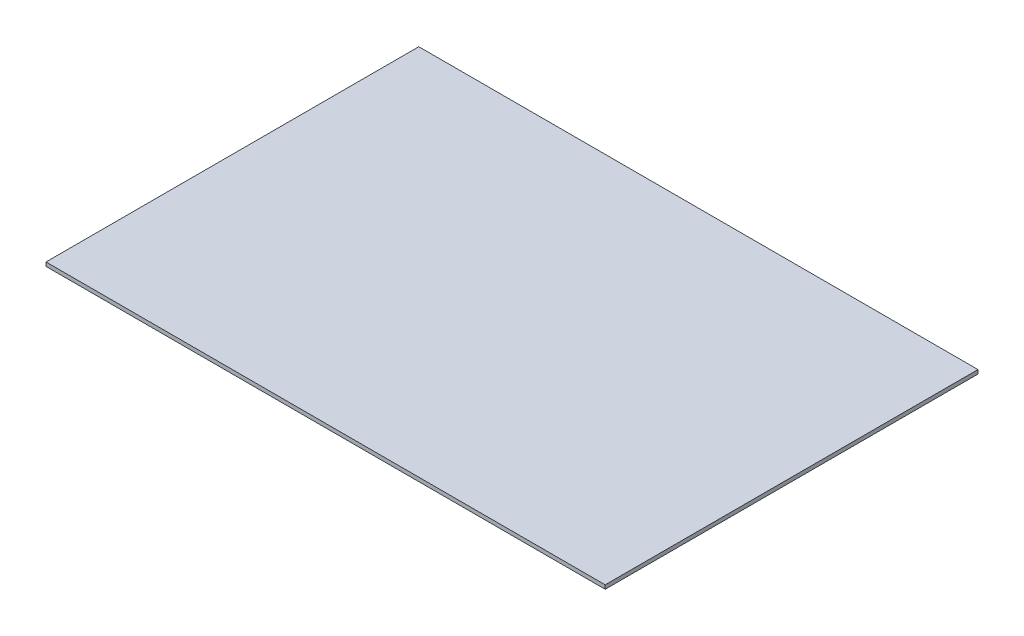
SolidWorks part; units mm, degrees
material "Acrylic (Medium-high impact)"
ref_plane "Front Plane" through (0, 0, 0) normal (0, 0, 1) x (1, 0, 0)
ref_plane "Top Plane" through (0, 0, 0) normal (0, 1, 0) x (1, 0, 0)
ref_plane "Right Plane" through (0, 0, 0) normal (1, 0, 0) x (0, 0, -1)
sketch "Sketch1" plane through (0, 0, 0) normal (0, 1, 0) x (1, 0, 0)
  line L1 (-228.6, -152.4) -> (228.6, -152.4)
  line L2 (-228.6, -152.4) -> (-228.6, 152.4)
  line L3 (-228.6, 152.4) -> (228.6, 152.4)
  line L4 (228.6, -152.4) -> (228.6, 152.4)
  line L5 (-228.6, -152.4) -> (228.6, 152.4) construction
  line L6 (-228.6, 152.4) -> (228.6, -152.4) construction
  point P0 (0, 0)
  dimension "D1" = 304.8
  dimension "D2" = 457.2
extrude "Boss-Extrude1" add sketch "Sketch1" along normal blind 3.175
